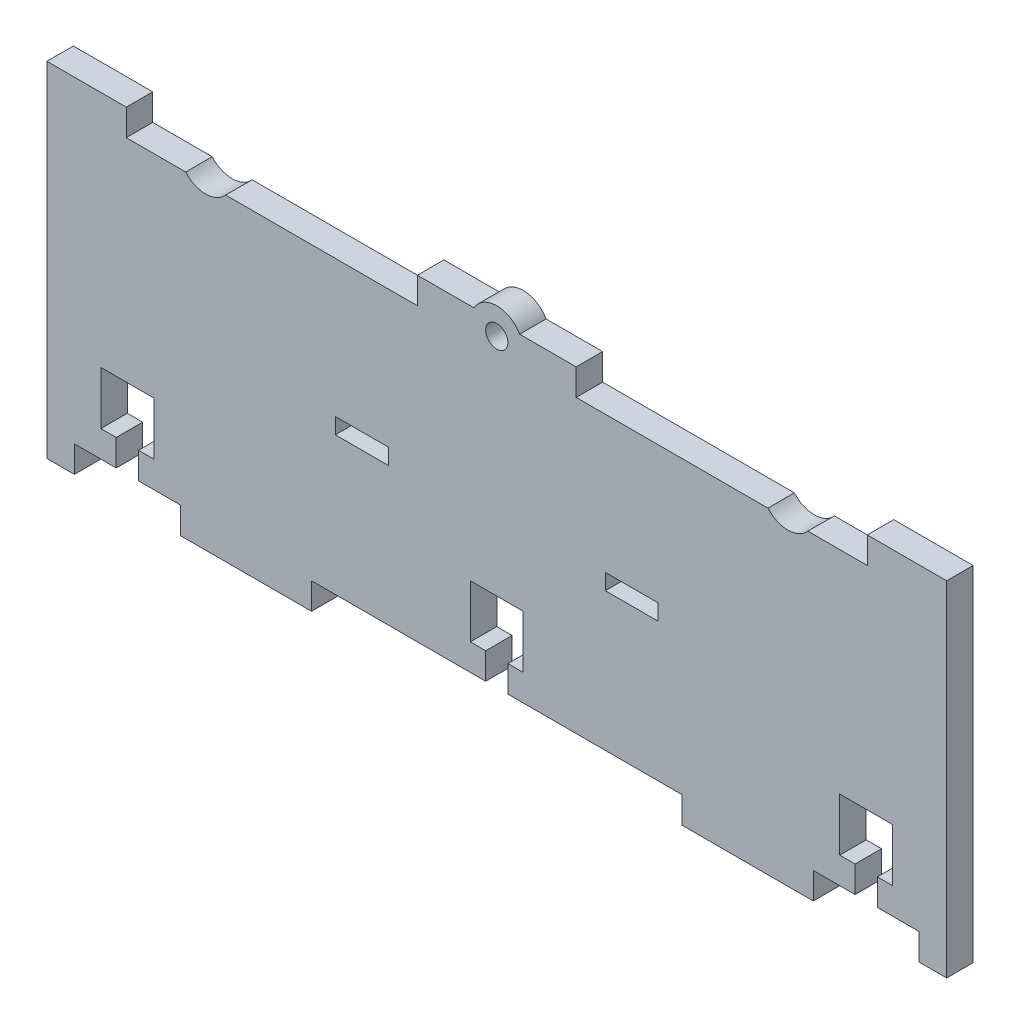
SolidWorks part; units mm, degrees
ref_plane "Front Plane" through (0, 0, 0) normal (0, 0, 1) x (1, 0, 0)
ref_plane "Top Plane" through (0, 0, 0) normal (0, 1, 0) x (1, 0, 0)
ref_plane "Right Plane" through (0, 0, 0) normal (1, 0, 0) x (0, 0, -1)
sketch "Sketch1" plane through (0, 0, 0) normal (0, 0, 1) x (1, 0, 0)
  line L0 (35, 0) -> (35, -5)
  line L1 (115, 0) -> (-115, 0)
  line L2 (0, 0) -> (0, 55) construction
  line L3 (115, 55) -> (-115, 55)
  line L4 (-115, 0) -> (-115, 55)
  line L5 (-115, 15) -> (-120, 15)
  line L6 (-115, 15) -> (-115, 40)
  line L7 (-115, 40) -> (-120, 40)
  line L8 (-120, 15) -> (-120, 40)
  line L9 (-100, 55) -> (-70, 55)
  line L10 (-100, 55) -> (-100, 60)
  line L11 (-100, 60) -> (-70, 60)
  line L12 (-70, 55) -> (-70, 60)
  line L13 (-95, 0) -> (-35, 0)
  line L14 (-95, 0) -> (-95, -5)
  line L15 (-95, -5) -> (-35, -5)
  line L16 (-35, 0) -> (-35, -5)
  line L17 (95, -5) -> (35, -5)
  line L18 (95, 0) -> (95, -5)
  line L19 (95, 0) -> (35, 0)
  line L20 (70, 55) -> (70, 60)
  line L21 (100, 60) -> (70, 60)
  line L22 (100, 55) -> (100, 60)
  line L23 (100, 55) -> (70, 55)
  line L24 (120, 15) -> (120, 40)
  line L25 (115, 40) -> (120, 40)
  line L26 (115, 15) -> (115, 40)
  line L27 (115, 15) -> (120, 15)
  line L28 (115, 0) -> (115, 55)
  point P9 (-120, 27.5)
  point P10 (0, 27.5)
  dimension "D1" = 115
  dimension "D2" = 55
  dimension "D3" = 5
  dimension "D4" = 25
  dimension "D5" = 30
  dimension "D6" = 15
  dimension "D7" = 5
  dimension "D8" = 5
  dimension "D9" = 60
  dimension "D10" = 20
extrude "Boss-Extrude1" add sketch "Sketch1" along normal blind 5 contours L1 L2 L3 L4 | L3 L22 L21 L20 | L18 L1 L0 L17 | L3 L12 L11 L10 | L16 L1 L14 L15 | L8 L5 L4 L7 | L26 L25 L24 L27
sketch "Sketch2" plane through (0, 0, 0) normal (0, 0, -1) x (-1, 0, 0)
  line L0 (120, 15) -> (120, 40) construction
  line L1 (85, -5) -> (120, -5)
  line L2 (85, -5) -> (85, 60)
  line L3 (85, 60) -> (120, 60)
  line L4 (120, -5) -> (120, 60)
  line L6 (95, -5) -> (35, -5) construction
  line L7 (0, 28.4281) -> (0, 15.5246) construction
  line L8 (-120, -5) -> (-120, 60)
  line L9 (-85, 60) -> (-120, 60)
  line L10 (-85, -5) -> (-85, 60)
  line L11 (-85, -5) -> (-120, -5)
  dimension "D1" = 35
  dimension "D2" = 35
  dimension "D3" = 65
extrude "Cut-Extrude1" cut sketch "Sketch2" against normal blind 10
sketch "Sketch3" plane through (0, 0, 0) normal (0, 0, -1) x (-1, 0, 0)
  line L0 (-70, 55) -> (70, 55) construction
  line L1 (-58.7707, 55) -> (-51.2293, 55)
  line L2 (0, 55) -> (0, 47.8155) construction
  line L3 (58.7707, 55) -> (51.2293, 55)
  line L5 (85, 60) -> (85, -5) construction
  arc A0 (-58.7707, 55) -> (-51.2293, 55) centre (-55, 58.2836) ccw
  arc A2 (58.7707, 55) -> (51.2293, 55) centre (55, 58.2836) cw
  line M7 (70, 55) -> (-70, 55)
  dimension "D1" = 5
  dimension "D2" = 26.2293
  dimension "D3" = 30
extrude "Cut-Extrude2" cut sketch "Sketch3" against normal blind 5 contours A2 M7 | L1 A0
sketch "Sketch4" plane through (0, 55, 0) normal (0, 1, 0) x (1, 0, 0)
  line L0 (51.2293, 0) -> (-51.2293, 0) construction
  line L1 (15, 0) -> (-15, 0)
  line L2 (15, 0) -> (15, -5)
  line L3 (15, -5) -> (-15, -5)
  line L4 (-15, 0) -> (-15, -5)
  line L5 (51.2293, -5) -> (-51.2293, -5) construction
  point P8 (0, 0)
  dimension "D1" = 30
  dimension "D2" = 15
extrude "Boss-Extrude2" add sketch "Sketch4" along normal blind 5
sketch "Sketch5" plane through (0, 0, 0) normal (0, 0, -1) x (-1, 0, 0)
  line L0 (-85, -5) -> (-35, -5) construction
  line L1 (-59.8, -5) -> (-79.8, -5)
  line L2 (-59.8, -5) -> (-59.8, 0)
  line L3 (-59.8, 0) -> (-79.8, 0)
  line L4 (-79.8, -5) -> (-79.8, 0)
  line L5 (-85, -5) -> (-85, 60) construction
  line L6 (0, 0) -> (0, 22.2278) construction
  line L7 (-35, 0) -> (35, 0) construction
  line L8 (79.8, -5) -> (79.8, 0)
  line L9 (59.8, 0) -> (79.8, 0)
  line L10 (59.8, -5) -> (59.8, 0)
  line L11 (59.8, -5) -> (79.8, -5)
  dimension "D1" = 20
  dimension "D2" = 5.2
extrude "Cut-Extrude3" cut sketch "Sketch5" against normal blind 5
sketch "Sketch6" plane through (0, 0, 0) normal (0, 0, -1) x (-1, 0, 0)
  line L0 (-15, 60) -> (15, 60) construction
  circle A0 centre (0, 57.5) radius 2.1
  dimension "D1" = 2.5
  dimension "D2" = 4.2
extrude "Cut-Extrude4" cut sketch "Sketch6" against normal blind 5
sketch "Sketch7" plane through (0, 0, 0) normal (0, 0, -1) x (-1, 0, 0)
  line L0 (-15, 60) -> (15, 60) construction
  line L1 (4.3301, 60) -> (-4.3301, 60)
  arc A0 (-4.3301, 60) -> (4.3301, 60) centre (0, 57.5) cw
  dimension "D1" = 5
extrude "Boss-Extrude3" add sketch "Sketch7" against normal blind 5
sketch "Sketch8" plane through (0, 0, 0) normal (0, 0, -1) x (-1, 0, 0)
  line L0 (79.8, 0) -> (59.8, 0) construction
  line L1 (67.7, 0) -> (71.9, 0)
  line L2 (67.7, 0) -> (67.7, 5)
  line L3 (67.7, 5) -> (71.9, 5)
  line L4 (71.9, 0) -> (71.9, 5)
  line L5 (0, 0) -> (0, 16.7932) construction
  line L6 (74.8, 5) -> (64.8, 5)
  line L7 (74.8, 5) -> (74.8, 15)
  line L8 (74.8, 15) -> (64.8, 15)
  line L9 (64.8, 5) -> (64.8, 15)
  line L10 (-64.8, 5) -> (-64.8, 15)
  line L11 (-74.8, 15) -> (-64.8, 15)
  line L12 (-74.8, 5) -> (-74.8, 15)
  line L13 (-74.8, 5) -> (-64.8, 5)
  line L14 (-71.9, 0) -> (-71.9, 5)
  line L15 (-67.7, 5) -> (-71.9, 5)
  line L16 (-67.7, 0) -> (-67.7, 5)
  line L17 (-67.7, 0) -> (-71.9, 0)
  line L18 (-35, 0) -> (35, 0) construction
  line L19 (-2.1, 0) -> (2.1, 0)
  line L20 (-2.1, 0) -> (-2.1, 5)
  line L21 (-2.1, 5) -> (2.1, 5)
  line L22 (2.1, 0) -> (2.1, 5)
  line L24 (-5, 5) -> (5, 5)
  line L25 (-5, 5) -> (-5, 15)
  line L26 (-5, 15) -> (5, 15)
  line L27 (5, 5) -> (5, 15)
  point P10 (69.8, 5)
  point P11 (69.8, 0)
  point P12 (69.8, 15)
  point P34 (0, 15)
  point P35 (0, 0)
  line M19 (-79.8, 0) -> (-59.8, 0)
  line M23 (-35, 0) -> (35, 0)
  line M27 (59.8, 0) -> (79.8, 0)
  dimension "D1" = 5
  dimension "D2" = 4.2
  dimension "D3" = 10
  dimension "D4" = 10
  dimension "D5" = 5
  dimension "D6" = 10
  dimension "D7" = 10
  dimension "D8" = 4.2
extrude "Cut-Extrude5" cut sketch "Sketch8" against normal blind 5 contours L12 L13 L10 L11 | L16 L13 L14 M19 | L5 L24 L27 L26 | L21 L5 L26 L25 L24 | L5 L19 L22 L24 | L5 L21 L20 M23 | L9 L6 L3 L7 L8 | L4 L3 L2 M27
sketch "Sketch9" plane through (0, 0, 0) normal (0, 0, -1) x (-1, 0, 0)
  line L0 (-20.5, 27.7965) -> (-42.5, 27.7965) construction
  line L1 (-20.5, 27.7965) -> (-42.5, 27.7965) construction
  line L2 (0, 57.5) -> (0, 41.2875) construction
  line L3 (-30.5, 26.1252) -> (-20.5, 26.1252)
  line L4 (-30.5, 26.1252) -> (-30.5, 29.1252)
  line L5 (-30.5, 29.1252) -> (-20.5, 29.1252)
  line L6 (-20.5, 26.1252) -> (-20.5, 29.1252)
  line L7 (20.5, 26.1252) -> (20.5, 29.1252)
  line L8 (30.5, 29.1252) -> (20.5, 29.1252)
  line L9 (30.5, 26.1252) -> (30.5, 29.1252)
  line L10 (30.5, 26.1252) -> (20.5, 26.1252)
  point P12 (0, 0)
  dimension "D1" = 3
  dimension "D2" = 10
extrude "Cut-Extrude6" cut sketch "Sketch9" against normal blind 10
